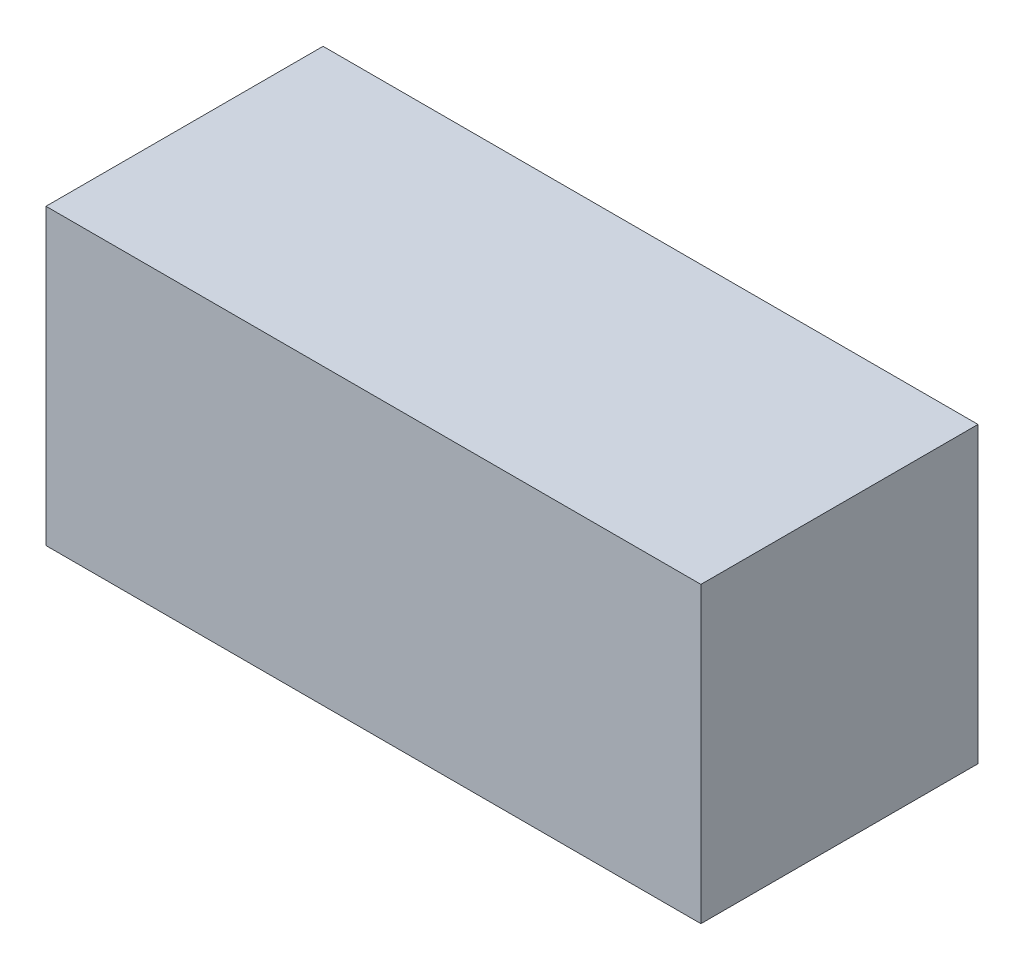
SolidWorks part; units mm, degrees
ref_plane "Plan de face" through (0, 0, 0) normal (0, 0, 1) x (1, 0, 0)
ref_plane "Plan de dessus" through (0, 0, 0) normal (0, 1, 0) x (1, 0, 0)
ref_plane "Plan de droite" through (0, 0, 0) normal (1, 0, 0) x (0, 0, -1)
sketch "Esquisse1" plane through (0, 0, 0) normal (0, 0, 1) x (1, 0, 0)
  line L1 (0, 0) -> (78, 0)
  line L2 (0, 0) -> (0, 35)
  line L3 (0, 35) -> (78, 35)
  line L4 (78, 0) -> (78, 35)
  dimension "D1" = 78
  dimension "D2" = 35
extrude "Boss.-Extru.1" add sketch "Esquisse1" along normal blind 33
